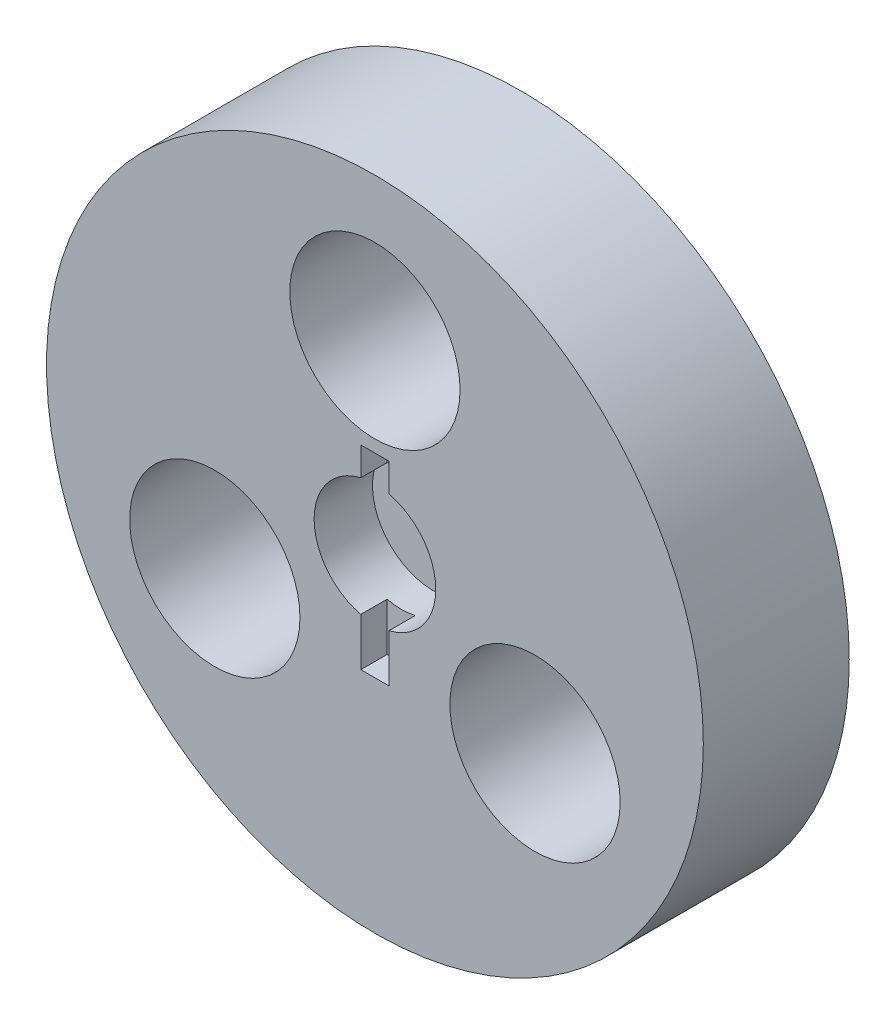
SolidWorks part; units mm, degrees
material "Teak"
ref_plane "Front Plane" through (0, 0, 0) normal (0, 0, 1) x (1, 0, 0)
ref_plane "Top Plane" through (0, 0, 0) normal (0, 1, 0) x (1, 0, 0)
ref_plane "Right Plane" through (0, 0, 0) normal (1, 0, 0) x (0, 0, -1)
sketch "Sketch1" plane through (0, 0, 0) normal (0, 0, 1) x (1, 0, 0)
  line L0 (0, 0) -> (20.8972, -12.065) construction
  line L1 (0, 42.8625) -> (0, -42.8625) construction
  line L2 (0, 0) -> (-20.8972, -12.065) construction
  line L3 (0, 24.13) -> (0, 0)
  circle A0 centre (0, 0) radius 42.8625
  circle A1 centre (0, 24.13) radius 11.1125
  circle A2 centre (-20.8972, -12.065) radius 11.1125
  circle A3 centre (20.8972, -12.065) radius 11.1125
  dimension "D3" = 85.725
  dimension "D5" = 22.225
  dimension "D1" = 120
  dimension "D2" = 120
  dimension "D4" = 24.13
extrude "Boss-Extrude1" add sketch "Sketch1" along normal mid plane 19.05
sketch "Sketch2" plane through (0, 0, 9.525) normal (0, 0, 1) x (1, 0, 0)
  circle A0 centre (0, 0) radius 7.9375
  dimension "D1" = 15.875
extrude "Cut-Extrude1" cut sketch "Sketch2" against normal blind 7.62
sketch "Sketch3" plane through (0, 0, 9.525) normal (0, 0, 1) x (1, 0, 0)
  line L0 (0, 11.43) -> (0, -13.97) construction
  line L1 (1.8415, 11.43) -> (-1.8415, 11.43)
  line L2 (1.8415, 11.43) -> (1.8415, -13.97)
  line L3 (1.8415, -13.97) -> (-1.8415, -13.97)
  line L4 (-1.8415, 11.43) -> (-1.8415, -13.97)
  circle A0 centre (0, 24.13) radius 11.1125 construction
  dimension "D1" = 3.683
  dimension "D2" = 25.4
  dimension "D3" = 12.7
extrude "Cut-Extrude2" cut sketch "Sketch3" against normal blind 3.429
